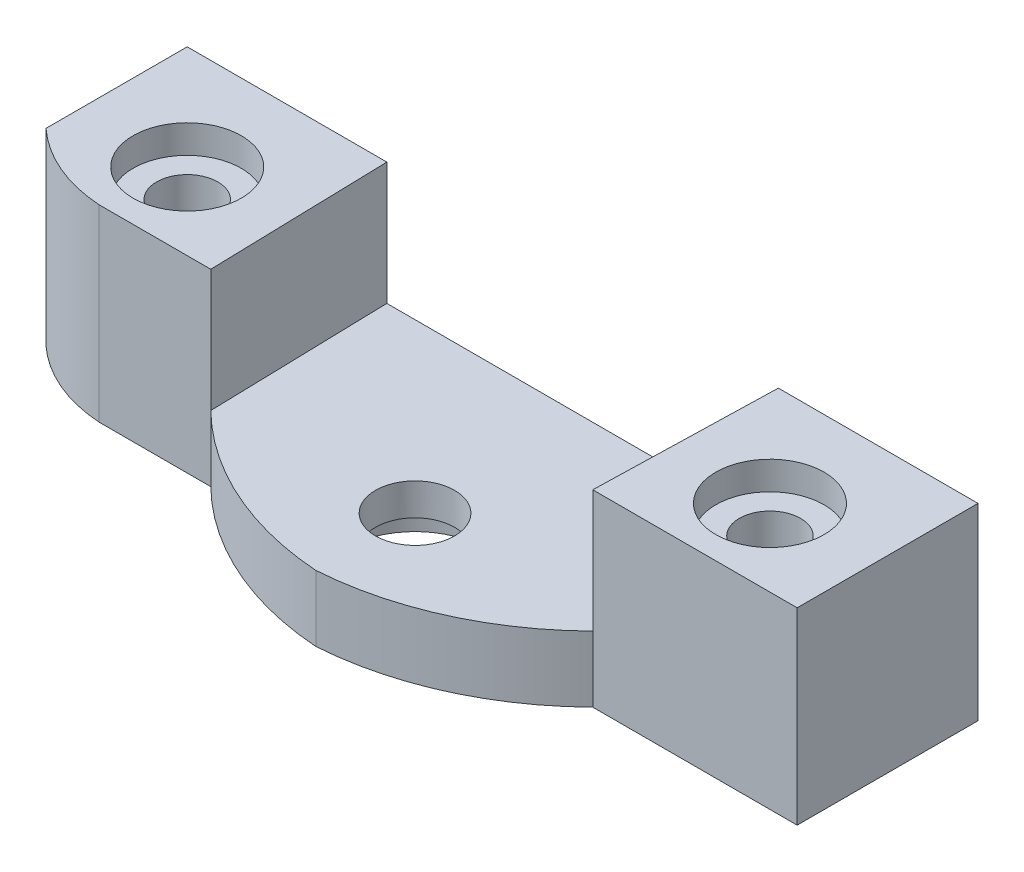
SolidWorks part; units mm, degrees
ref_plane "Front Plane" through (0, 0, 0) normal (0, 0, 1) x (1, 0, 0)
ref_plane "Top Plane" through (0, 0, 0) normal (0, 1, 0) x (1, 0, 0)
ref_plane "Right Plane" through (0, 0, 0) normal (1, 0, 0) x (0, 0, -1)
sketch "Sketch1" plane through (0, 0, 0) normal (0, 1, 0) x (1, 0, 0)
  line L0 (-15.475, -0.525) -> (15.475, -0.525) construction
  line L1 (-21, 5) -> (21, 5)
  line L2 (-21, 5) -> (-21, -5)
  line L3 (-21, -5) -> (21, -5)
  line L4 (21, 5) -> (21, -5)
  line L5 (-21, 5) -> (21, -5) construction
  line L6 (-21, -5) -> (21, 5) construction
  circle A0 centre (-15.475, -0.525) radius 1.625
  circle A1 centre (15.475, -0.525) radius 1.625
  point P0 (0, 0)
  point P9 (0, 0)
  point P11 (-15.475, 1.1)
  dimension "D4" = 3.25
  dimension "D5" = 3.25
  dimension "D1" = 10
  dimension "D2" = 42
  dimension "D3" = 30.95
  dimension "D6" = 3.9
extrude "Boss-Extrude1" add sketch "Sketch1" along normal blind 10
sketch "Sketch2" plane through (0, 10, 0) normal (0, 1, 0) x (1, 0, 0)
  line L0 (-21, -5) -> (21, -5) construction
  circle A0 centre (0, -5) radius 10.1522
extrude "Cut-Extrude2" cut sketch "Sketch2" against normal blind 6.5
sketch "Sketch3" plane through (0, 3.5, 0) normal (0, 1, 0) x (1, 0, 0)
  line L1 (-21, -5) -> (21, -5)
  line L2 (-21, -5) -> (-21, -4.917)
  line L3 (-9.6058, -4.917) -> (9.6058, -4.917)
  line L5 (-21, -4.917) -> (-21, -4.6052)
  line L6 (-21, 5) -> (-21, -5) construction
  line L7 (-21, -4.6052) -> (-9.6058, -4.6052)
  line L8 (-9.6058, -4.6052) -> (-9.6058, -4.917)
  line L9 (0, 5) -> (0, 2.8913) construction
  line L10 (1.7512, 5) -> (-1.7512, 5) construction
  line L11 (9.6058, -4.6052) -> (9.6058, -4.917)
  line L12 (21, -4.6052) -> (9.6058, -4.6052)
  line L13 (21, -5) -> (21, -4.6052)
extrude "Cut-Extrude3" cut sketch "Sketch3" along normal mid plane 20
sketch "Sketch4" plane through (0, 10, 0) normal (0, 1, 0) x (1, 0, 0)
  line L3 (0, 5) -> (0, 2.5885) construction
  line L4 (1.7512, 5) -> (-1.7512, 5) construction
  circle A0 centre (-15.475, -0.525) radius 2.875
  circle A2 centre (15.475, -0.525) radius 2.875
  dimension "D1" = 5.75
extrude "Cut-Extrude4" cut sketch "Sketch4" against normal blind 1.5
sketch "Sketch6" plane through (0, 3.5, 0) normal (0, 1, 0) x (1, 0, 0)
  line L0 (-10.1445, -4.6052) -> (-10.3967, 5)
  line L1 (-1.7512, 5) -> (-21, 5) construction
  line L2 (-10.3967, 5) -> (-1.7512, 5)
  line L3 (0, 5) -> (0, 3.6678) construction
  line L4 (1.7512, 5) -> (-1.7512, 5) construction
  line L5 (10.1445, -4.6052) -> (10.3967, 5)
  line L6 (10.3967, 5) -> (1.7512, 5)
  arc A0 (-10.1445, -4.6052) -> (-1.7512, 5) centre (0, -5) cw
  arc A1 (10.1445, -4.6052) -> (1.7512, 5) centre (0, -5) ccw
extrude "Cut-Extrude5" cut sketch "Sketch6" along normal blind 8
sketch "Sketch9" plane through (0, 0, 0) normal (0, 1, 0) x (1, 0, 0)
  line L0 (0, -4.917) -> (0, -9.167) construction
  line L1 (-9.6058, -4.917) -> (9.6058, -4.917) construction
  line L2 (-10.1445, -4.6052) -> (-9.6058, -4.6052)
  line L3 (-9.6058, -4.6052) -> (-9.6058, -4.917)
  line L4 (-9.6058, -4.917) -> (9.6058, -4.917)
  line L5 (9.6058, -4.6052) -> (9.6058, -4.917)
  line L6 (10.1445, -4.6052) -> (9.6058, -4.6052)
  arc A0 (0, -9.167) -> (-10.1445, -4.6052) centre (1.0926, 6.8233) cw
  arc A1 (0, -9.167) -> (10.1445, -4.6052) centre (-1.0926, 6.8233) ccw
  dimension "D1" = 4.25
extrude "Boss-Extrude6" add sketch "Sketch9" along normal blind 3.5
sketch "Sketch10" plane through (0, 3.5, 0) normal (0, 1, 0) x (1, 0, 0)
  line L0 (0, 5) -> (0, -3.9) construction
  line L1 (10.3967, 5) -> (-10.3967, 5) construction
  circle A2 centre (0, -3.9) radius 2.1
  dimension "D2" = 4.2
  dimension "D1" = 8.9
extrude "Cut-Extrude6" cut sketch "Sketch10" against normal blind 4.5
sketch "Sketch12" plane through (0, 10, 0) normal (0, 1, 0) x (1, 0, 0)
  line L0 (-21, -4.6052) -> (-21, -2.4999)
  line L1 (-21, 5) -> (-21, -4.6052) construction
  line L2 (-21, -4.6052) -> (-16.0708, -4.6052)
  arc A0 (-16.0708, -4.6052) -> (-21, -2.4999) centre (-15.5718, 3.3865) cw
extrude "Cut-Extrude8" cut sketch "Sketch12" against normal blind 10
sketch "Sketch13" plane through (0, 0, 0) normal (0, -1, 0) x (1, 0, 0)
  circle A0 centre (0, 3.9) radius 3.75
  dimension "D1" = 7.5
extrude "Cut-Extrude9" cut sketch "Sketch13" against normal blind 1.8 contours A0
